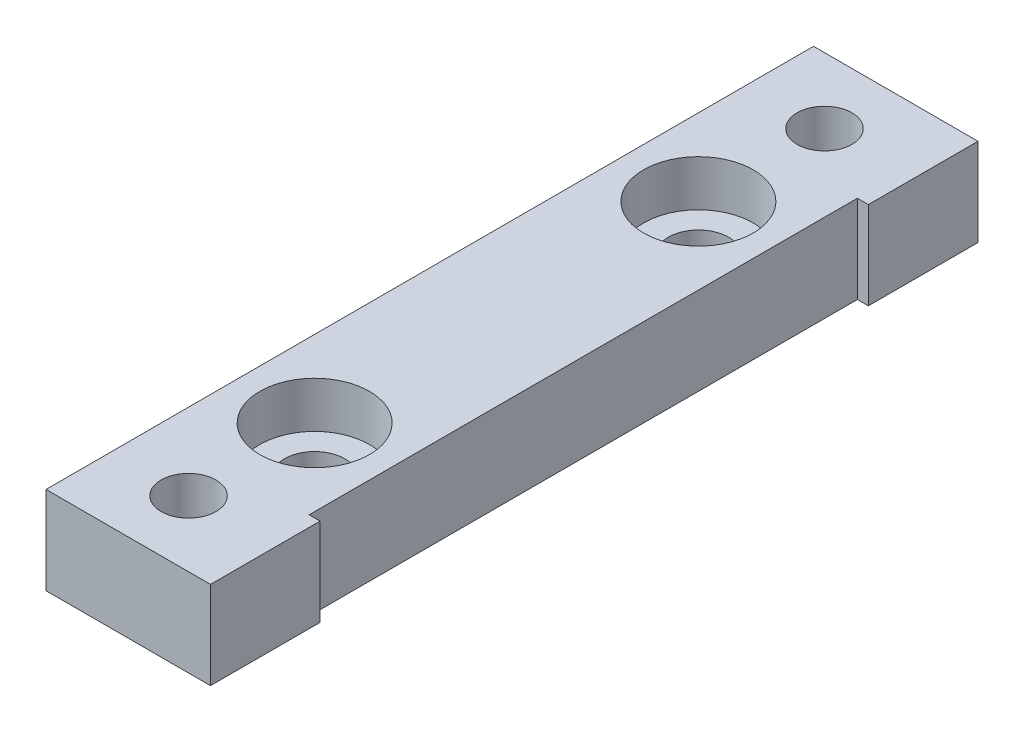
SolidWorks part; units mm, degrees
ref_plane "Front Plane" through (0, 0, 0) normal (0, 0, 1) x (1, 0, 0)
ref_plane "Top Plane" through (0, 0, 0) normal (0, 1, 0) x (1, 0, 0)
ref_plane "Right Plane" through (0, 0, 0) normal (1, 0, 0) x (0, 0, -1)
sketch "Sketch1" plane through (0, 0, 0) normal (0, 1, 0) x (1, 0, 0)
  line L1 (-7.5, 35) -> (7.5, 35)
  line L2 (-7.5, 35) -> (-7.5, -35)
  line L3 (-7.5, -35) -> (7.5, -35)
  line L4 (7.5, 35) -> (7.5, -35)
  line L5 (-7.5, 35) -> (7.5, -35) construction
  line L6 (-7.5, -35) -> (7.5, 35) construction
  point P0 (0, 0)
  dimension "D1" = 15
  dimension "D2" = 70
extrude "Boss-Extrude1" add sketch "Sketch1" along normal blind 8
sketch "Sketch2" plane through (0, 8, 0) normal (0, 1, 0) x (1, 0, 0)
  line L0 (7.5, -35) -> (7.5, 35) construction
  line L1 (7.5, 25) -> (6.5, 25)
  line L2 (7.5, 25) -> (7.5, -25)
  line L3 (7.5, -25) -> (6.5, -25)
  line L4 (6.5, 25) -> (6.5, -25)
  line L5 (-7.5, -35) -> (7.5, -35) construction
  line L6 (7.5, 35) -> (-7.5, 35) construction
  dimension "D1" = 1
  dimension "D2" = 10
  dimension "D3" = 10
extrude "Cut-Extrude1" cut sketch "Sketch2" against normal blind 8
sketch "Sketch3" plane through (0, 8, 0) normal (0, 1, 0) x (1, 0, 0)
  line L0 (-7.5, 35) -> (-7.5, -35) construction
  line L1 (7.5, 35) -> (-7.5, 35) construction
  line L2 (-7.5, -35) -> (7.5, -35) construction
  circle A0 centre (-0.5, -29) radius 2.5
  circle A1 centre (-0.5, 29) radius 2.5
  dimension "D1" = 7
  dimension "D2" = 6
  dimension "D3" = 6
  dimension "D4" = 7
extrude "Cut-Extrude2" cut sketch "Sketch3" against normal blind 8
sketch "Sketch4" plane through (0, 8, 0) normal (0, 1, 0) x (1, 0, 0)
  line L0 (-7.5, 35) -> (-7.5, -35) construction
  line L1 (-7.5, -35) -> (7.5, -35) construction
  line L2 (7.5, 35) -> (-7.5, 35) construction
  circle A0 centre (-0.5, -17.5) radius 2.75
  circle A1 centre (-0.5, 17.5) radius 2.75
  point P6 (0, 0)
  dimension "D1" = 7
  dimension "D2" = 7
  dimension "D3" = 17.5
  dimension "D4" = 17.5
extrude "Cut-Extrude3" cut sketch "Sketch4" against normal blind 8
sketch "Sketch5" plane through (0, 8, 0) normal (0, 1, 0) x (1, 0, 0)
  circle A0 centre (-0.5, 17.5) radius 5
  circle A1 centre (-0.5, -17.5) radius 5
extrude "Cut-Extrude4" cut sketch "Sketch5" against normal blind 4.2
